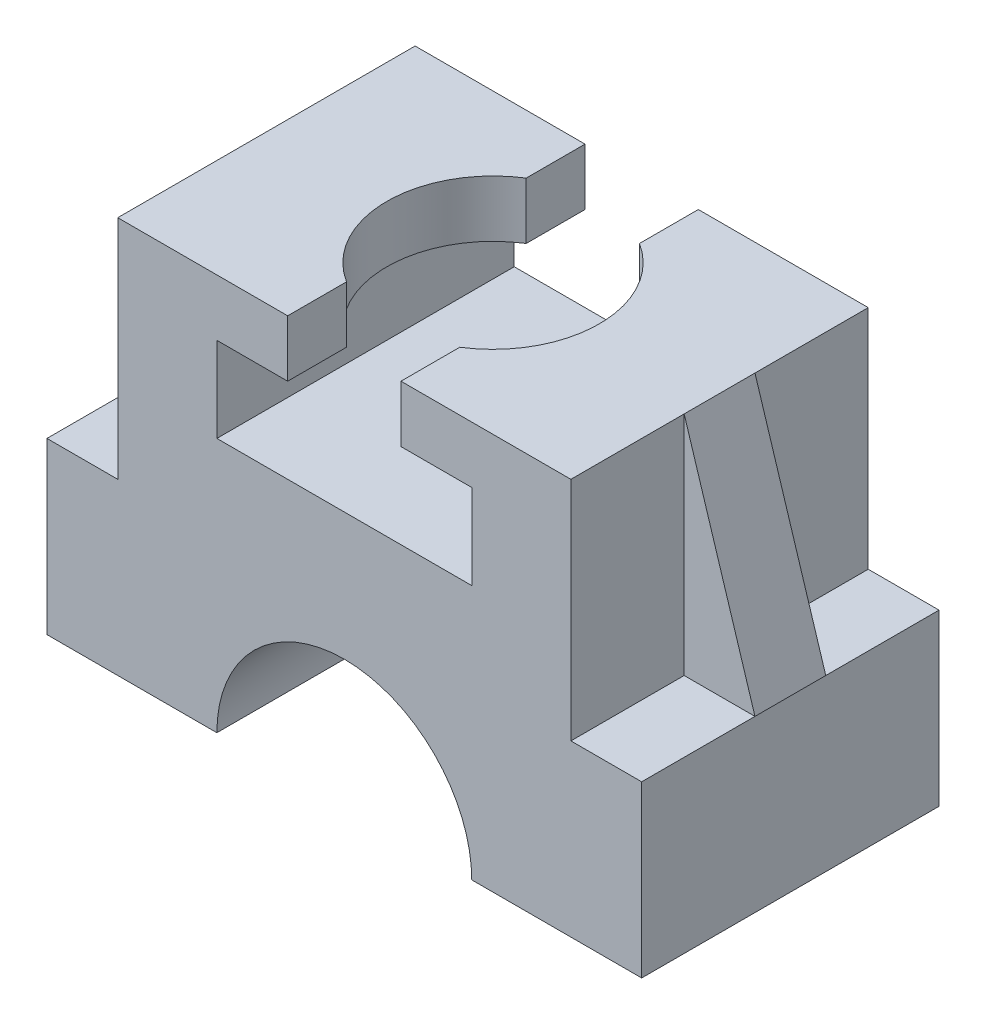
SolidWorks part; units mm, degrees
ref_plane "Front Plane" through (0, 0, 0) normal (0, 0, 1) x (1, 0, 0)
ref_plane "Top Plane" through (0, 0, 0) normal (0, 1, 0) x (1, 0, 0)
ref_plane "Right Plane" through (0, 0, 0) normal (1, 0, 0) x (0, 0, -1)
sketch "Sketch1" plane through (0, 0, 0) normal (0, 0, 1) x (1, 0, 0)
  line L0 (0, 241.0371) -> (0, 90) construction
  line L1 (-435.4461, 0) -> (403.8593, 0) construction
  line L2 (45, 0) -> (105, 0)
  line L3 (105, 0) -> (105, 60)
  line L4 (105, 60) -> (80, 60)
  line L5 (80, 60) -> (80, 140)
  line L6 (80, 140) -> (20, 140)
  line L7 (20, 140) -> (20, 120)
  line L8 (-45, 90) -> (45, 90)
  line L9 (45, 90) -> (45, 120)
  line L10 (45, 120) -> (20, 120)
  line L12 (435.4461, 0) -> (-403.8593, 0) construction
  line L13 (-45, 120) -> (-20, 120)
  line L14 (-45, 90) -> (-45, 120)
  line L15 (-20, 140) -> (-20, 120)
  line L16 (-80, 140) -> (-20, 140)
  line L17 (-80, 60) -> (-80, 140)
  line L18 (-105, 60) -> (-80, 60)
  line L19 (-105, 0) -> (-105, 60)
  line L20 (-45, 0) -> (-105, 0)
  line L21 (0, 45) -> (0, -265.8553) construction
  arc A0 (45, 0) -> (-45, 0) centre (0, 0) ccw
  dimension "D1" = 90
  dimension "D2" = 60
  dimension "D3" = 60
  dimension "D4" = 25
  dimension "D5" = 80
  dimension "D6" = 60
  dimension "D7" = 20
  dimension "D8" = 30
  dimension "D9" = 45
extrude "Boss-Extrude1" add sketch "Sketch1" along normal mid plane 105 contours L13 L15 L16 L17 L18 L19 L20 A0 L2 L3 L4 L5 L6 L7 L10 L9 L8 L14
sketch "Sketch2" plane through (0, 140, 0) normal (0, 1, 0) x (1, 0, 0)
  circle A0 centre (0, 0) radius 37.5
  dimension "D1" = 75
extrude "Cut-Extrude1" cut sketch "Sketch2" against normal up to next
sketch "Sketch3" plane through (0, 0, 0) normal (0, 0, 1) x (1, 0, 0)
  line L0 (105, 60) -> (80, 60)
  line L1 (80, 60) -> (80, 140)
  line L2 (80, 60) -> (80, 140) construction
  line L3 (80, 140) -> (105, 60)
  dimension "D1" = 80
  dimension "D2" = 25
extrude "Boss-Extrude2" add sketch "Sketch3" along normal mid plane 25
sketch "Sketch4" plane through (0, 0, 0) normal (0, 0, 1) x (1, 0, 0)
  line L0 (-105, 60) -> (-80, 60)
  line L1 (-80, 60) -> (-80, 140)
  line L2 (-80, 60) -> (-80, 140) construction
  line L3 (-80, 140) -> (-105, 60)
  dimension "D1" = 80
  dimension "D2" = 25
extrude "Boss-Extrude3" add sketch "Sketch4" along normal mid plane 25
